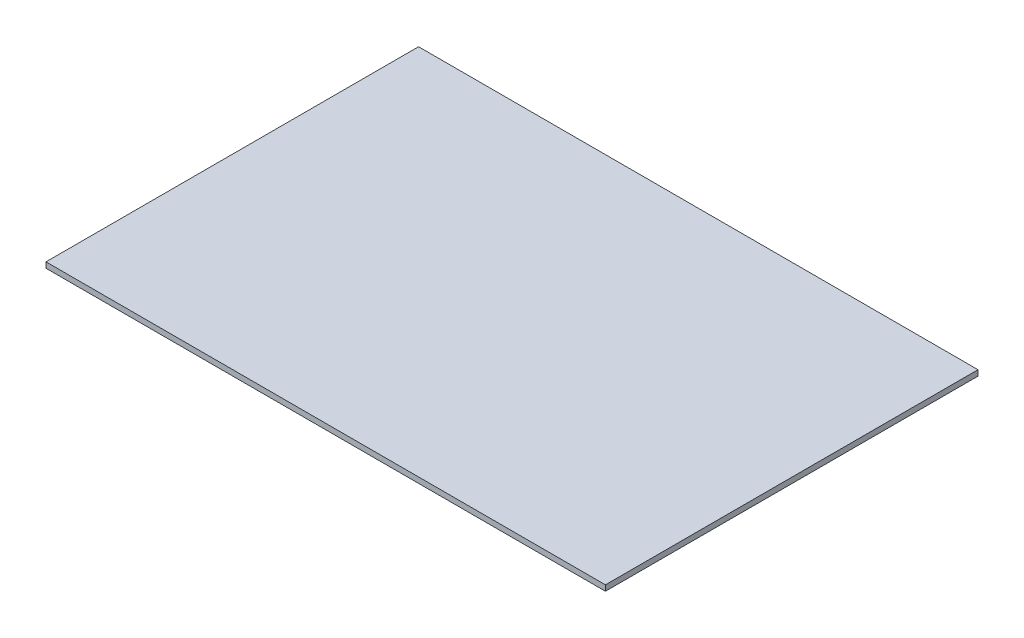
SolidWorks part; units mm, degrees
ref_plane "Face" through (0, 0, 0) normal (0, 0, 1) x (1, 0, 0)
ref_plane "Dessus" through (0, 0, 0) normal (0, 1, 0) x (1, 0, 0)
ref_plane "Droite" through (0, 0, 0) normal (1, 0, 0) x (0, 0, -1)
sketch "Esquisse1" plane through (0, 0, 0) normal (0, 1, 0) x (1, 0, 0)
  line L1 (0, 0) -> (1000, 0)
  line L2 (0, 0) -> (0, 666)
  line L3 (0, 666) -> (1000, 666)
  line L4 (1000, 0) -> (1000, 666)
  dimension "D1" = 666
  dimension "D2" = 1000
extrude "Extrusion1" add sketch "Esquisse1" along normal blind 10
